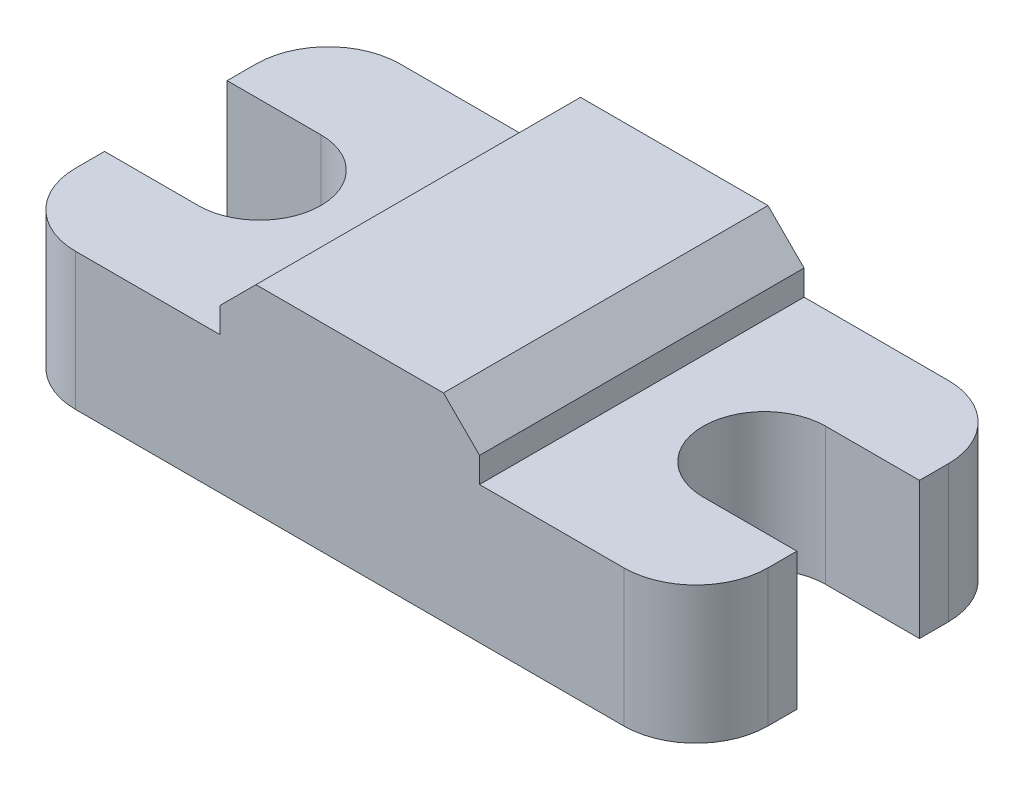
SolidWorks part; units mm, degrees
ref_plane "Front Plane" through (0, 0, 0) normal (0, 0, 1) x (1, 0, 0)
ref_plane "Top Plane" through (0, 0, 0) normal (0, 1, 0) x (1, 0, 0)
ref_plane "Right Plane" through (0, 0, 0) normal (1, 0, 0) x (0, 0, -1)
sketch "Sketch1" plane through (0, 0, 0) normal (0, 1, 0) x (1, 0, 0)
  line L0 (0, 6.2) -> (2.6, 6.2)
  line L1 (2, 0) -> (17.2, 0)
  line L2 (0, 2) -> (0, 2.8)
  line L3 (2, 9) -> (17.2, 9)
  line L4 (19.2, 2) -> (19.2, 2.8)
  line L5 (0, 2.8) -> (2.6, 2.8)
  line L6 (19.2, 6.2) -> (16.6, 6.2)
  line L7 (19.2, 2.8) -> (16.6, 2.8)
  line L8 (0, 6.2) -> (0, 7)
  line L9 (19.2, 6.2) -> (19.2, 7)
  arc A0 (2.6, 2.8) -> (2.6, 6.2) centre (2.6, 4.5) ccw
  arc A1 (16.6, 6.2) -> (16.6, 2.8) centre (16.6, 4.5) ccw
  arc A2 (2, 0) -> (0, 2) centre (2, 2) cw
  arc A3 (17.2, 0) -> (19.2, 2) centre (17.2, 2) ccw
  arc A4 (17.2, 9) -> (19.2, 7) centre (17.2, 7) cw
  arc A5 (0, 7) -> (2, 9) centre (2, 7) cw
  point P17 (3.7804, 4.4463)
  point P18 (3.8709, 3.315)
  point P19 (3.5615, 5.6705)
  point P20 (14.2943, 3.4527)
  point P21 (14.348, 6.5034)
  point P22 (0, 0)
  point P27 (19.2, 9)
  point P30 (0, 9)
  dimension "D5" = 2.8
  dimension "D6" = 2.8
  dimension "D7" = 2.6
  dimension "D8" = 2.6
  dimension "D9" = 2
  dimension "D1" = 9
  dimension "D2" = 19.2
  dimension "D3" = 3.4
  dimension "D4" = 3.4
extrude "Boss-Extrude1" add sketch "Sketch1" along normal blind 3.8
sketch "Sketch3" plane through (0, 3.8, 0) normal (0, 1, 0) x (1, 0, 0)
  line L0 (17.2, 9) -> (2, 9) construction
  line L1 (13.2, 9) -> (6, 9)
  line L2 (13.2, 9) -> (13.2, 0)
  line L3 (13.2, 0) -> (6, 0)
  line L4 (6, 9) -> (6, 0)
  line L5 (2, 0) -> (17.2, 0) construction
  line L6 (0, 7) -> (0, 6.2) construction
  point P10 (0, 6.6)
  dimension "D1" = 6
  dimension "D2" = 7.2
extrude "Boss-Extrude2" add sketch "Sketch3" along normal blind 1.7
chamfer "Chamfer1" distance 1 angle 45 2 edges at (13.2, 5.5, -4.5) (6, 5.5, -4.5)
